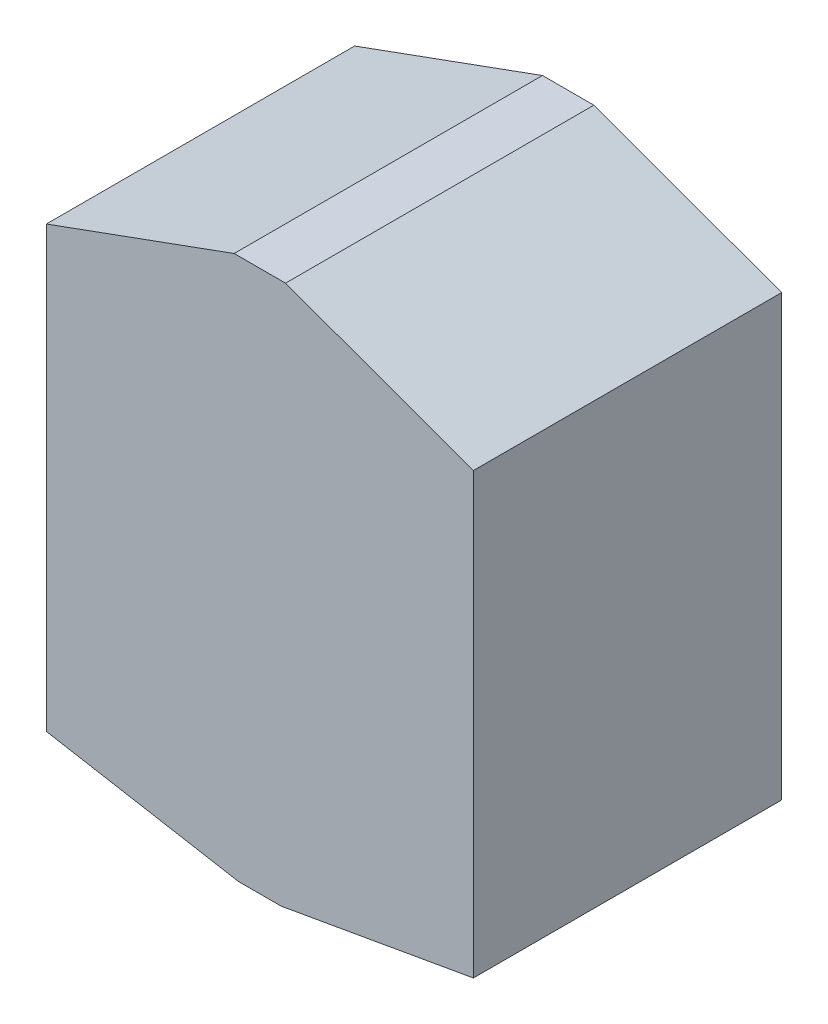
SolidWorks part; units mm, degrees
ref_plane "Front Plane" through (0, 0, 0) normal (0, 0, 1) x (1, 0, 0)
ref_plane "Top Plane" through (0, 0, 0) normal (0, 1, 0) x (1, 0, 0)
ref_plane "Right Plane" through (0, 0, 0) normal (1, 0, 0) x (0, 0, -1)
sketch "Sketch1" plane through (0, 0, 0) normal (0, 0, 1) x (1, 0, 0)
  line L0 (25, 271.1086) -> (-25, 271.1086) construction
  line L1 (20.7767, 218.3949) -> (-20.7767, 218.3949) construction
  line L2 (0, 289.0237) -> (0, -12.8882) construction
  line L3 (-25, 271.1086) -> (-20.7767, 218.3949) construction
  line L4 (25, 271.1086) -> (20.7767, 218.3949) construction
  line L5 (-20.7767, 218.3949) -> (-20.7767, 271.1086) construction
  line L6 (20.7767, 218.3949) -> (20.7767, 271.1086) construction
  line L7 (3.2655, -0.1757) -> (-3.2655, -0.1757) construction
  line L8 (-2.5, 271.1086) -> (-0.3266, -0.1757) construction
  line L9 (2.5, 271.1086) -> (0.3266, -0.1757) construction
  line L10 (17.2669, 174.5862) -> (-17.2669, 174.5862) construction
  line L11 (-2.0777, 218.3949) -> (-20.7767, 221.6921) construction
  line L12 (2.0777, 218.3949) -> (20.7767, 221.6921) construction
  line L13 (-20.7767, 218.3949) -> (-17.2669, 174.5862) construction
  line L14 (20.7767, 218.3949) -> (17.2669, 174.5862) construction
  line L15 (-17.2669, 174.5862) -> (-17.2669, 218.3949) construction
  line L16 (17.2669, 174.5862) -> (17.2669, 218.3949) construction
  line L17 (-2.0777, 218.3949) -> (-17.2669, 212.8665) construction
  line L18 (-1.7267, 174.5862) -> (-17.2669, 177.3264) construction
  line L19 (1.7267, 174.5862) -> (17.2669, 177.3264) construction
  line L20 (2.0777, 218.3949) -> (17.2669, 212.8665) construction
  line L37 (-2.5, 271.1086) -> (-20.7767, 264.4564) construction
  line L38 (2.5, 271.1086) -> (20.7767, 264.4564) construction
  line L39 (-2.5, 271.1086) -> (-20.7767, 264.4564)
  line L40 (-20.7767, 264.4564) -> (-20.7767, 221.6921)
  line L41 (-20.7767, 221.6921) -> (-2.0777, 218.3949)
  line L42 (-2.0777, 218.3949) -> (2.0777, 218.3949)
  line L43 (2.0777, 218.3949) -> (20.7767, 221.6921)
  line L44 (20.7767, 221.6921) -> (20.7767, 264.4564)
  line L45 (20.7767, 264.4564) -> (2.5, 271.1086)
  line L46 (2.5, 271.1086) -> (-2.5, 271.1086)
  spline S0 degree 3 poles (0, -0.1757) (0, 2.6446) (0, 8.7879) (0, 18.9298) (0, 31.0627) (0, 45.6618) (0, 63.2285) (0, 84.366) (0, 109.8) (0, 140.3454) (0, 177.1117) (0, 221.3632) (0, 253.5373) (0, 271.1086) knots 0 0 0 0 0.031188 0.067936 0.112154 0.16536 0.229381 0.306415 0.399109 0.510644 0.644202 0.805689 1 1 1 1
  point P19 (0, 218.3949)
  point P24 (-0.3266, -0.1757)
  point P25 (-2.5, 271.1086)
  point P26 (0.3266, -0.1757)
  point P27 (2.5, 271.1086)
  point P32 (-2.0777, 218.3949)
  point P34 (-1.7267, 174.5862)
  point P35 (-1.4364, 138.3538)
  point P36 (-1.194, 108.0962)
  point P37 (-0.9925, 82.95)
  point P38 (-0.8251, 62.0517)
  point P39 (-0.5703, 30.2499)
  point P40 (0, 44.6838)
  point P41 (-0.686, 44.6838)
  point P42 (-0.4742, 18.2543)
  point P43 (-0.3943, 8.2851)
  point P44 (2.0777, 218.3949)
  point P45 (1.7267, 174.5862)
  point P46 (1.4364, 138.3538)
  point P47 (1.194, 108.0962)
  point P48 (0.9925, 82.95)
  point P49 (0.8251, 62.0517)
  point P50 (0.686, 44.6838)
  point P51 (0.5703, 30.2499)
  point P52 (0.4742, 18.2543)
  point P53 (0.3943, 8.2851)
  point P60 (0, 174.5862)
  dimension "D1" = 50
  dimension "D2" = 41.5535
  dimension "D3" = 6.531
  dimension "D4" = 0.6531
  dimension "D5" = 5
  dimension "D6" = 10
  dimension "D7" = 34.5338
  dimension "D8" = 20
  dimension "D9" = 10
  dimension "D10" = 20
extrude "Boss-Extrude1" add sketch "Sketch1" along normal blind 30 contours L42 S0 L46 L39 L40 L41 | S0 L42 L43 L44 L45 L46
